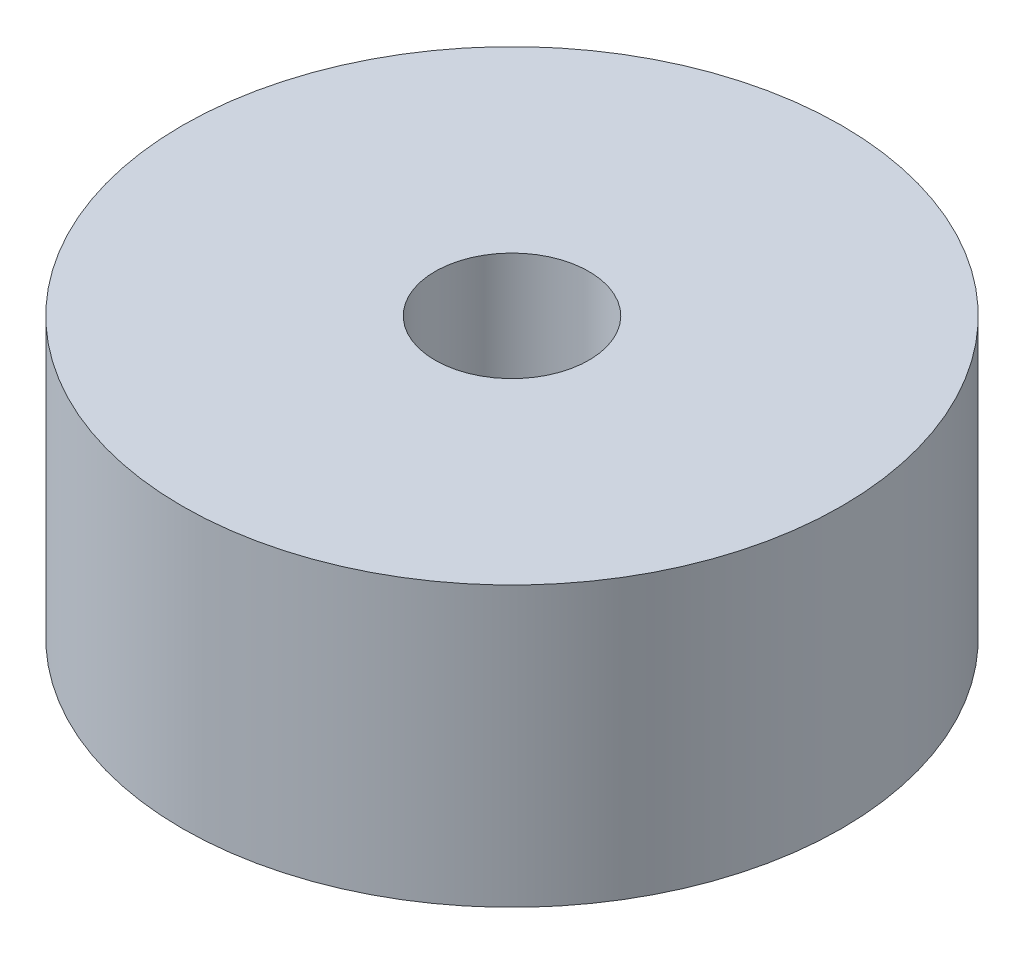
SolidWorks part; units mm, degrees
ref_plane "Front Plane" through (0, 0, 0) normal (0, 0, 1) x (1, 0, 0)
ref_plane "Top Plane" through (0, 0, 0) normal (0, 1, 0) x (1, 0, 0)
ref_plane "Right Plane" through (0, 0, 0) normal (1, 0, 0) x (0, 0, -1)
sketch "Sketch1" plane through (0, 0, 0) normal (0, 1, 0) x (1, 0, 0)
  circle A0 centre (0, 0) radius 7.5
  dimension "D1" = 15
extrude "Boss-Extrude1" add sketch "Sketch1" along normal blind 6.35
sketch "Sketch2" plane through (0, 6.35, 0) normal (0, 1, 0) x (1, 0, 0)
  circle A0 centre (0, 0) radius 1.75
  dimension "D1" = 3.5
extrude "Cut-Extrude1" cut sketch "Sketch2" against normal through all
